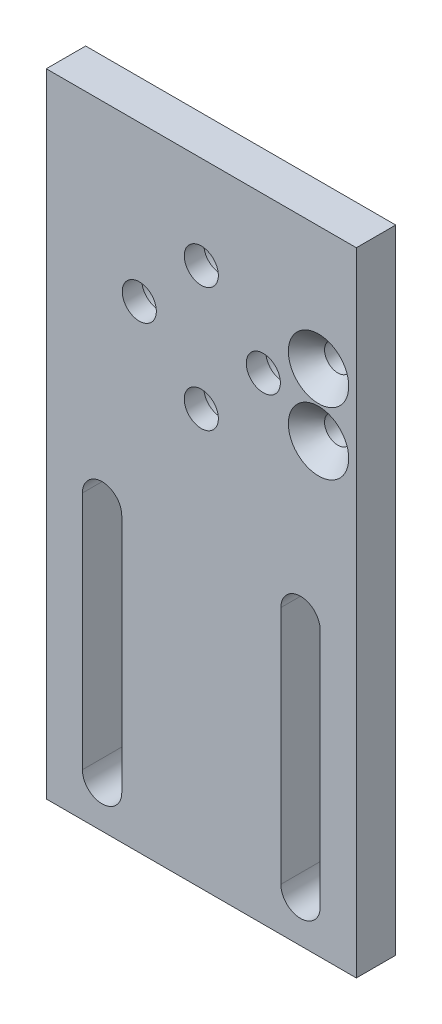
SolidWorks part; units mm, degrees
ref_plane "Front Plane" through (0, 0, 0) normal (0, 0, 1) x (1, 0, 0)
ref_plane "Top Plane" through (0, 0, 0) normal (0, 1, 0) x (1, 0, 0)
ref_plane "Right Plane" through (0, 0, 0) normal (1, 0, 0) x (0, 0, -1)
sketch "Sketch1" plane through (0, 0, 0) normal (0, 0, 1) x (1, 0, 0)
  line L0 (44.4384, -76.9874) -> (44.4384, -83.9724)
  line L1 (25, -25) -> (-25, -25)
  line L2 (25, -25) -> (25, 25)
  line L3 (25, 25) -> (-25, 25)
  line L4 (-25, -25) -> (-25, 25)
  line L5 (10, -10) -> (-10, -10)
  line L6 (10, -10) -> (10, 10)
  line L7 (10, 10) -> (-10, 10)
  line L8 (-10, -10) -> (-10, 10)
  line L9 (10, -10) -> (-10, 10) construction
  line L10 (10, 10) -> (-10, -10) construction
  line L11 (71.5527, -76.9874) -> (29.6427, -76.9874)
  line L12 (71.5527, -76.9874) -> (71.5527, -48.9966)
  line L13 (0, -62.992) -> (0, -88.392)
  line L15 (71.5527, -48.9966) -> (29.6427, -48.9966)
  line L16 (29.6427, -76.9874) -> (29.6427, -48.9966)
  line L17 (71.5527, -76.9874) -> (29.6427, -48.9966) construction
  line L18 (71.5527, -48.9966) -> (29.6427, -76.9874) construction
  line L19 (50.5977, -83.9724) -> (50.5977, -113.9724)
  line L20 (0, 0) -> (0, -62.992) construction
  line L21 (-25, -76.9874) -> (25, -76.9874)
  line L23 (56.7571, -83.9724) -> (44.4384, -83.9724)
  line L24 (0, -88.392) -> (-18.1627, -88.392)
  line L29 (66.5972, -69.9897) -> (34.5983, -69.9897)
  line L30 (66.5972, -69.9897) -> (66.5972, -55.9943)
  line L31 (66.5972, -55.9943) -> (34.5983, -55.9943)
  line L32 (34.5983, -69.9897) -> (34.5983, -55.9943)
  line L33 (66.5972, -69.9897) -> (34.5983, -55.9943) construction
  line L34 (66.5972, -55.9943) -> (34.5983, -69.9897) construction
  line L35 (56.7571, -76.9874) -> (56.7571, -83.9724)
  line L38 (0, -88.392) -> (0, -113.792)
  line L39 (0, -113.792) -> (-34.158, -113.792)
  line L40 (-25, -25) -> (-25, -76.9874)
  line L42 (25, -76.9874) -> (25, -25)
  line L43 (-16.002, -31.3415) -> (-16.002, -69.9897) construction
  line L44 (-12.827, -31.3415) -> (-12.827, -69.9897)
  line L45 (-19.177, -31.3415) -> (-19.177, -69.9897)
  line L46 (16.002, -31.3415) -> (16.002, -69.9897) construction
  line L47 (19.177, -31.3415) -> (19.177, -69.9897)
  line L48 (12.827, -31.3415) -> (12.827, -69.9897)
  arc A6 (-12.827, -31.3415) -> (-19.177, -31.3415) centre (-16.002, -31.3415) ccw
  arc A7 (-19.177, -69.9897) -> (-12.827, -69.9897) centre (-16.002, -69.9897) ccw
  circle A8 centre (34.5983, -55.9943) radius 2.667
  circle A9 centre (34.5983, -69.9897) radius 2.667
  circle A10 centre (66.5972, -69.9897) radius 2.667
  circle A11 centre (66.5972, -55.9943) radius 2.667
  arc A12 (19.177, -31.3415) -> (12.827, -31.3415) centre (16.002, -31.3415) ccw
  arc A13 (12.827, -69.9897) -> (19.177, -69.9897) centre (16.002, -69.9897) ccw
  point P0 (0, 0)
  point P18 (0, 0)
  point P20 (50.5977, -62.992)
  point P39 (50.5977, -62.992)
  point P46 (50.5977, -62.992)
  point P65 (-16.002, -50.6656)
  point P70 (16.002, -50.6656)
  dimension "D1" = 32.004
  dimension "D2" = 16.002
  dimension "D3" = 16.002
extrude "Boss-Extrude1" add sketch "Sketch1" along normal blind 6.35
hole_wizard "CSK for #6 Flat Head Machine Screw2" positions "Sketch12" profile "Sketch9" countersink size "#6" standard "ANSI Inch" end condition through all
sketch "Sketch12" plane through (0, 0, 6.35) normal (0, 0, 1) x (1, 0, 0)
  line L1 (25, -76.9874) -> (25, 25) construction
  point P18 (18.904, 5.0482)
  point P20 (18.904, -5.0482)
  dimension "D2" = 6.096
  dimension "D1" = 6.096
  dimension "D7" = 5.0482
  dimension "D8" = 5.0482
sketch "Sketch9" plane through (18.904, 5.0482, 6.35) normal (1, 0, 0) x (0, -1, 0)
  line L0 (0, 0) -> (0, 6.35)
  line L1 (0, 6.35) -> (2.1526, 6.35)
  line L2 (2.1526, 6.35) -> (2.1526, 3.1238)
  line L3 (2.1526, 3.1238) -> (4.8681, 0)
  line L5 (4.8681, 0) -> (0, 0)
  line L6 (-2.1526, 3.1238) -> (-4.8681, 0) construction
  line L11 (0, -6.35) -> (0, 107.95) construction
  dimension "Thru Hole Dia." = 4.3053
  dimension "Thru Hole Depth" = 6.35
  dimension "Near C'Sink Dia." = 9.7362
  dimension "Near C'Sink Angle" = 82
hole_wizard "CBORE for M5 SHCS1" positions "Sketch14" profile "Sketch13" counterbore size "M5" standard "ANSI Metric" end condition through all
sketch "Sketch14" plane through (0, 0, 0) normal (0, 0, -1) x (-1, 0, 0)
  line L2 (0, 10) -> (-10, 0)
  line L3 (-10, 0) -> (0, -10)
  line L4 (0, -10) -> (10, 0)
  line L5 (10, 0) -> (0, 10)
  line L6 (0, 0) -> (0, 10)
  circle A0 centre (0, 0) radius 7.0711 construction
  point P13 (0, 10)
  point P14 (-10, 0)
  point P15 (0, -10)
  point P16 (10, 0)
sketch "Sketch13" plane through (0, 10, 0) normal (1, 0, 0) x (0, 1, 0)
  line L0 (0, 0) -> (0, 6.35)
  line L1 (0, 6.35) -> (2.75, 6.35)
  line L3 (2.75, 6.35) -> (2.75, 3.2)
  line L4 (2.75, 3.2) -> (5, 3.2)
  line L5 (5, 3.2) -> (5, 0)
  line L7 (5, 0) -> (0, 0)
  line L11 (0, -6.35) -> (0, 107.95) construction
  dimension "Thru Hole Dia." = 5.5
  dimension "Thru Hole Depth" = 6.35
  dimension "C'Bore Dia." = 10
  dimension "C'Bore Depth" = 3.2
